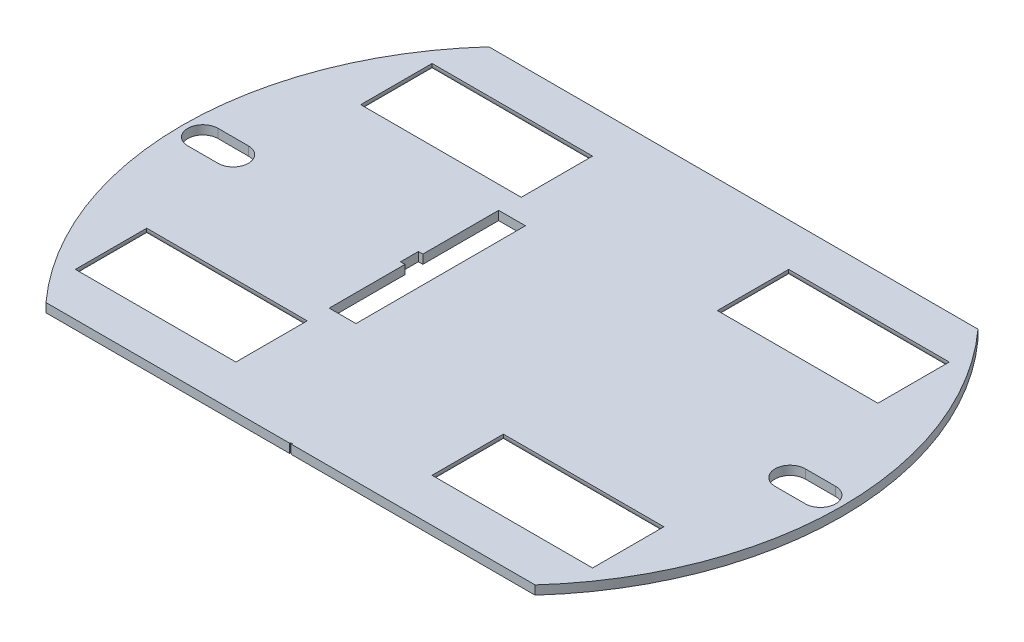
SolidWorks part; units mm, degrees
ref_plane "Płaszczyzna przednia" through (0, 0, 0) normal (0, 0, 1) x (1, 0, 0)
ref_plane "Płaszczyzna górna" through (0, 0, 0) normal (0, 1, 0) x (1, 0, 0)
ref_plane "Płaszczyzna prawa" through (0, 0, 0) normal (1, 0, 0) x (0, 0, -1)
sketch "Sketch1" plane through (0, 0, 0) normal (0, 1, 0) x (1, 0, 0)
  line L8 (0, 0) -> (0, 37)
  line L9 (0, 0) -> (0, -37)
  line L11 (0, 37) -> (0, 24.8373)
  line L14 (0, 24.8373) -> (27.4246, 24.8373)
  line L15 (27.4246, 24.8373) -> (-27.4246, 24.8373)
  line L16 (27.4246, 24.8373) -> (27.4246, -24.8373)
  line L17 (27.4246, -24.8373) -> (-27.4246, -24.8373)
  circle A0 centre (0, 0) radius 37
  point P0 (0, 0)
extrude "Boss-Extrude1" add sketch "Sketch1" along normal blind 2
sketch "Sketch2" plane through (0, 0, 0) normal (0, -1, 0) x (1, 0, 0)
  line L0 (0, 0) -> (-8, 0)
  line L6 (-8, 0) -> (-8, 9.5)
  line L7 (-8, 9.5) -> (-11, 9.5)
  line L8 (-11, 9.5) -> (-11, -9.5)
  line L9 (-11, -9.5) -> (-8, -9.5)
  line L10 (-8, -9.5) -> (-8, 0)
  line L11 (-8, 0) -> (-8, 1)
  line L12 (-8, 1) -> (-11.5, 1)
  line L13 (-11.5, 1) -> (-11.5, -1)
  line L14 (-11.5, -1) -> (-8, -1)
  line L15 (-8, -1) -> (-8, 1)
extrude "Cut-Extrude1" cut sketch "Sketch2" against normal blind 22 contours L6 L7 L8 L9 L10 | L12 L13 L14 L15
sketch "Sketch3" plane through (0, 2, 0) normal (0, 1, 0) x (1, 0, 0)
  line L0 (2.9, 0) -> (2.9, 10.1)
  line L1 (2.9, 10.1) -> (19, 10.1)
  line L2 (19, 10.1) -> (19, -10.1)
  line L3 (19, -10.1) -> (-14.6, -10.1)
  line L4 (-14.6, -10.1) -> (-14.6, 10.1)
  line L5 (-14.6, 10.1) -> (2.9, 10.1)
  line L6 (2.9, 10.1) -> (2.9, 11.6)
  line L7 (19, 10.1) -> (20.5, 10.1)
  line L8 (19, -10.1) -> (19, -11.6)
  line L9 (-14.6, -10.1) -> (-16.1, -10.1)
  line L10 (2.9, 11.6) -> (20.5, 11.6)
  line L11 (20.5, 11.6) -> (20.5, -11.6)
  line L12 (20.5, -11.6) -> (-16.1, -11.6)
  line L13 (-16.1, -11.6) -> (-16.1, 11.6)
  line L14 (-16.1, 11.6) -> (2.9, 11.6)
  line L15 (-14.6, 10.1) -> (-16.1, 10.1)
extrude "Boss-Extrude2" add sketch "Sketch3" along normal blind 7 contours L11 L10 L6 L1 L7 | L12 L11 L7 L2 L8 | L13 L12 L8 L3 L9 | L15 L5 L6 L14 L13
sketch "Sketch4" plane through (0, 0, 0) normal (0, -1, 0) x (1, 0, 0)
  line L0 (0, 0) -> (-8, 0)
  line L1 (-8, -9.5) -> (-8, 9.5) construction
  line L2 (-8, 0) -> (-8.023, 9.319)
  line L3 (-8.023, 9.319) -> (-3, 9.319)
  line L4 (-3, 9.319) -> (-3, -9.5)
  line L5 (-3, -9.5) -> (-8, -9.5)
  line L6 (-8, -9.5) -> (-8, 0)
extrude "Boss-Extrude3" add sketch "Sketch4" along normal blind 6 contours L2 L3 L4 L5 L6
sketch "Sketch5" plane through (-8, 0, 0) normal (-1, 0, 0) x (0, 0, 1)
  line L0 (0, 0) -> (0, -6)
  line L3 (-24.8373, 0) -> (24.8373, 0) construction
  line L5 (0, -6) -> (0, 0) construction
  circle A1 centre (-5.031, -2.35) radius 2.25
  circle A4 centre (5.031, -2.35) radius 2.25
extrude "Cut-Extrude3" cut sketch "Sketch5" against normal blind 37 and the other way blind 37 contours A1 | A4
fillet "Fillet1" radius 3 2 edges at (-5.5, -6, -9.5) (-5.5115, -6, 9.319)
fillet "Fillet2" radius 0.5 2 edges at (-37, 2, 0) (37, 2, 0)
sketch "Sketch6" plane through (0, 0, 0) normal (0, -1, 0) x (1, 0, 0)
  line L0 (0.0031, -0.031) -> (-32.9969, -0.031)
  line L1 (0.0031, -0.031) -> (-0.0115, 6.969)
  line L2 (-32.9969, -0.031) -> (-34.6969, -0.031)
  line L3 (-34.6969, -0.031) -> (-31.2969, -0.031)
  line L4 (-34.6969, 1.669) -> (-31.2969, 1.669)
  line L5 (-34.6969, -1.731) -> (-31.2969, -1.731)
  line L6 (33.0028, 0.1067) -> (0.0031, -0.031)
  line L7 (31.3028, 1.8067) -> (34.7028, 1.8067)
  line L9 (34.7028, -1.5933) -> (31.3028, -1.5933)
  circle A0 centre (-32.9969, -0.031) radius 1.7
  circle A1 centre (33.0028, 0.1067) radius 1.7
  circle A2 centre (-31.2969, -0.031) radius 1.7
  circle A3 centre (-34.6969, -0.031) radius 1.7
  arc A4 (-31.2969, 1.669) -> (-31.2969, -1.731) centre (-31.2969, -0.031) cw
  arc A5 (-34.6969, 1.669) -> (-34.6969, -1.731) centre (-34.6969, -0.031) ccw
  circle A8 centre (31.3028, 0.1067) radius 1.7
  circle A9 centre (34.7028, 0.1067) radius 1.7
  arc A10 (31.3028, 1.8067) -> (31.3028, -1.5933) centre (31.3028, 0.1067) ccw
  arc A15 (34.7028, 1.8067) -> (34.7028, -1.5933) centre (34.7028, 0.1067) cw
  dimension "D1" = 33
extrude "Cut-Extrude4" cut sketch "Sketch6" against normal blind 37 contours A1
fillet "Fillet3" radius 0.5 6 edges at (20.5, 9, 0) (19, 9, 0) (1.45, 9, -10.1) (2.2, 9, -11.6) (2.2, 9, 11.6) (1.45, 9, 10.1)
fillet "Fillet4" radius 0.5 10 edges at (-16.1, 5.25, 11.6) (-16.1, 8.8536, 11.4536) (-16.1, 9, 10.85) (-16.1, 8.8536, 10.2464) (-16.1, 5.25, -10.1) (-16.1, 8.8536, -10.2464) (-16.1, 9, -10.85) (-16.1, 8.8536, -11.4536) (-16.1, 5.25, 10.1) (-16.1, 5.25, -11.6)
sketch "Sketch7" plane through (0, 0, 0) normal (0, -1, 0) x (1, 0, 0)
  line L0 (0.0031, -0.031) -> (20.0031, -0.031)
  line L1 (20.0031, -0.031) -> (20.0031, 14.969)
  line L2 (20.0031, 14.969) -> (20.0031, 19.969)
  line L3 (20.0031, 19.969) -> (11.0031, 19.969)
  line L4 (11.0031, 19.969) -> (11.0031, 11.969)
  line L5 (11.0031, 11.969) -> (29.0031, 11.969)
  line L6 (29.0031, 11.969) -> (29.0031, 19.969)
  line L7 (29.0031, 19.969) -> (20.0031, 19.969)
  line L8 (0.0031, -0.031) -> (0.0031, 13.3164)
  line L9 (29.0031, -20.031) -> (20.0031, -20.031)
  line L10 (29.0031, -12.031) -> (29.0031, -20.031)
  line L11 (11.0031, -12.031) -> (29.0031, -12.031)
  line L12 (11.0031, -20.031) -> (11.0031, -12.031)
  line L13 (20.0031, -20.031) -> (11.0031, -20.031)
  line L14 (-28.9969, -12.031) -> (-28.9969, -20.031)
  line L15 (-10.9969, -12.031) -> (-28.9969, -12.031)
  line L16 (-10.9969, -20.031) -> (-10.9969, -12.031)
  line L17 (-19.9969, -20.031) -> (-10.9969, -20.031)
  line L18 (-28.9969, -20.031) -> (-19.9969, -20.031)
  line L19 (-28.9969, 19.969) -> (-19.9969, 19.969)
  line L20 (-28.9969, 11.969) -> (-28.9969, 19.969)
  line L21 (-10.9969, 11.969) -> (-28.9969, 11.969)
  line L22 (-10.9969, 19.969) -> (-10.9969, 11.969)
  line L23 (-19.9969, 19.969) -> (-10.9969, 19.969)
extrude "Cut-Extrude5" cut sketch "Sketch7" against normal blind 10 contours L23 L19 L20 L21 L22 | L4 L5 L1 L2 L3 | L6 L7 L2 L1 L5 | L14 L18 L17 L16 L15 | L13 L9 L10 L11 L12
fillet "Fillet8" radius 1 16 edges at (11.0031, 0, 15.969) (20.0031, 0, 11.969) (29.0031, 0, 15.969) (20.0031, 0, 19.969) (20.0031, 0, -12.031) (29.0031, 0, -16.031) (20.0031, 0, -20.031) (11.0031, 0, -16.031) (-10.9969, 0, 15.969) (-19.9969, 0, 19.969) (-28.9969, 0, 15.969) (-19.9969, 0, 11.969) (-28.9969, 0, -16.031) (-19.9969, 0, -12.031) (-19.9969, 0, -20.031) (-10.9969, 0, -16.031)
sketch "Sketch8" plane through (0, 0, 24.8373) normal (0, 0, 1) x (1, 0, 0)
  line L0 (0, 0) -> (0, 1)
  line L1 (0, 1) -> (46.8329, 1)
  line L2 (46.8329, 1) -> (-54.4517, 1)
  line L3 (0, 0) -> (-0.1, 0)
  line L4 (27.4246, 0) -> (-27.4246, 0) construction
  line L5 (-0.1, 0) -> (-0.1, 1)
  line L6 (-0.1, 1) -> (0.1, 1)
  line L7 (0.1, 1) -> (0.1, 0)
  line L8 (0.1, 0) -> (-0.1, 0)
  line M6 (-27.4246, 0) -> (27.4246, 0)
extrude "Cut-Extrude6" cut sketch "Sketch8" against normal blind 0.1 contours L5 L0 L2 M6 | L7 L1 L0 M6
sketch "Sketch10" plane through (0, 0, 0) normal (0, -1, 0) x (1, 0, 0)
  circle A0 centre (0, 0) radius 57.5567
sketch "Sketch11" plane through (0, 2, 0) normal (0, 1, 0) x (1, 0, 0)
  circle A0 centre (0, 0) radius 50.238
extrude "Cut-Extrude8" cut sketch "Sketch11" against normal blind 1 and the other way blind 11
